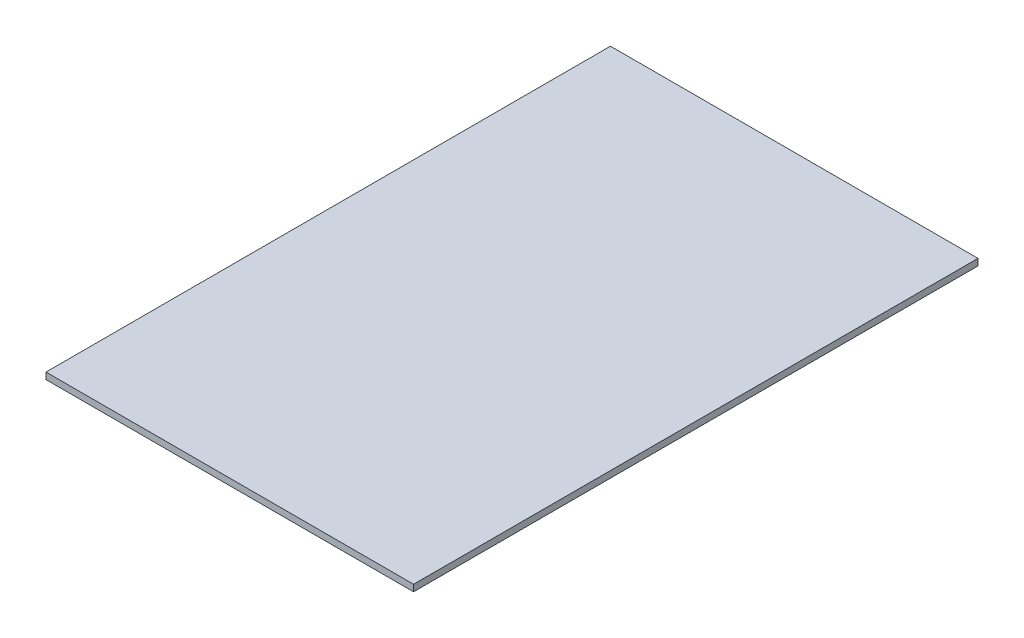
SolidWorks part; units mm, degrees
ref_plane "Alzado" through (0, 0, 0) normal (0, 0, 1) x (1, 0, 0)
ref_plane "Planta" through (0, 0, 0) normal (0, 1, 0) x (1, 0, 0)
ref_plane "Vista lateral" through (0, 0, 0) normal (1, 0, 0) x (0, 0, -1)
sketch "Croquis1" plane through (0, 0, 0) normal (0, 1, 0) x (1, 0, 0)
  line L1 (-70, -137.5) -> (70, -137.5)
  line L2 (-70, -137.5) -> (-70, 137.5)
  line L3 (-70, 137.5) -> (70, 137.5)
  line L4 (70, -137.5) -> (70, 137.5)
  line L5 (-70, -137.5) -> (70, 137.5) construction
  line L6 (-70, 137.5) -> (70, -137.5) construction
  point P0 (0, 0)
  dimension "D1" = 140
  dimension "D2" = 275
extrude "Saliente-Extruir1" add sketch "Croquis1" along normal blind 2.5
sketch "Croquis2" plane through (0, 0, 0) normal (0, -1, 0) x (-1, 0, 0)
  line L0 (35, -137.5) -> (35, 137.5) construction
  line L1 (70, -137.5) -> (-70, -137.5) construction
  line L2 (0, -137.5) -> (0, 137.5) construction
  line L3 (-70, 137.5) -> (70, 137.5) construction
  line L4 (-35, -137.5) -> (-35, 137.5) construction
  line L5 (70, 0) -> (-70, 0) construction
  line L6 (70, 137.5) -> (70, -137.5) construction
  line L7 (-70, -137.5) -> (-70, 137.5) construction
  line L8 (70, 35) -> (-70, 35) construction
  line L9 (70, -35) -> (-70, -35) construction
  line L18 (56, -18) -> (14, -18)
  line L19 (56, 18) -> (56, -18)
  line L20 (56, 18) -> (14, 18)
  line L21 (14, 18) -> (14, -18)
  line L22 (-14, 18) -> (-14, -18)
  line L23 (-56, 18) -> (-14, 18)
  line L24 (-56, 18) -> (-56, -18)
  line L25 (-56, -18) -> (-14, -18)
  dimension "D5" = 42
  dimension "D6" = 36
  dimension "D7" = 42
  dimension "D8" = 36
  dimension "D9" = 18
  dimension "D10" = 21
  dimension "D11" = 18
  dimension "D12" = 14
  dimension "D1" = 35
  dimension "D2" = 35
  dimension "D3" = 35
  dimension "D4" = 35
extrude "Saliente-Extruir2" add sketch "Croquis2" along normal blind 1
sketch "Croquis3" plane through (0, 2.5, 0) normal (0, 1, 0) x (1, 0, 0)
  line L5 (70, -137.5) -> (70, 137.5) construction
  line L6 (-70, 137.5) -> (70, 137.5)
  line L7 (-70, 137.5) -> (-70, 77.5)
  line L8 (-70, 77.5) -> (70, 77.5)
  line L9 (70, 137.5) -> (70, 77.5)
  dimension "D1" = 60
extrude "Cortar-Extruir1" cut sketch "Croquis3" against normal through all
